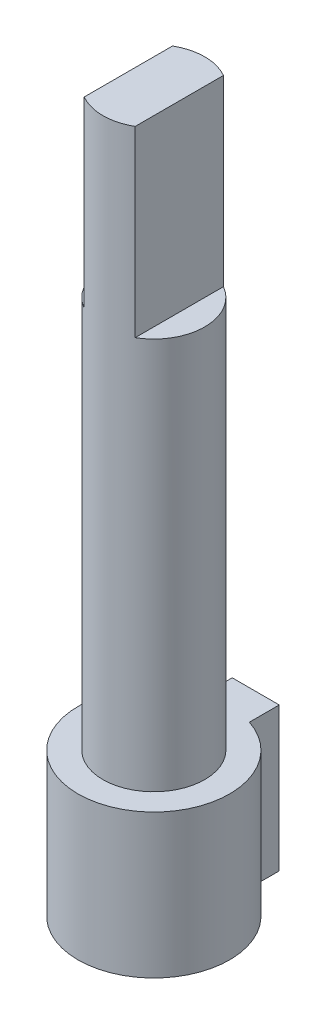
SolidWorks part; units mm, degrees
ref_plane "Front Plane" through (0, 0, 0) normal (0, 0, 1) x (1, 0, 0)
ref_plane "Top Plane" through (0, 0, 0) normal (0, 1, 0) x (1, 0, 0)
ref_plane "Right Plane" through (0, 0, 0) normal (1, 0, 0) x (0, 0, -1)
sketch "Sketch1" plane through (0, 0, 0) normal (0, 1, 0) x (1, 0, 0)
  line L1 (-1, 2.8284) -> (1, 2.8284)
  line L2 (-1, 2.8284) -> (-1, 3.9984)
  line L3 (-1, 3.9984) -> (1, 3.9984)
  line L4 (1, 2.8284) -> (1, 3.9984)
  circle A0 centre (0, 0) radius 3
  point P7 (0, 0)
  point P8 (0, 2.8284)
  dimension "D1" = 6
  dimension "D2" = 1.17
  dimension "D3" = 2
extrude "Boss-Extrude1" add sketch "Sketch1" along normal blind 27.5 contours L1 A0
sketch "Sketch2" plane through (0, 27.5, 0) normal (0, 1, 0) x (1, 0, 0)
  circle A0 centre (0, 0) radius 1.95
  circle A1 centre (0, 0) radius 6.1662
  dimension "D1" = 3.9
extrude "Cut-Extrude1" cut sketch "Sketch2" against normal blind 22
sketch "Sketch3" plane through (0, 27.5, 0) normal (0, 1, 0) x (1, 0, 0)
  line L0 (-0.975, 1.6887) -> (-0.975, -1.6887)
  line L1 (0.975, 1.6887) -> (0.975, -1.6887)
  circle A0 centre (0, 0) radius 1.95 construction
  arc A1 (-0.975, 1.6887) -> (-0.975, -1.6887) centre (0, 0) ccw
  arc A2 (0.975, -1.6887) -> (0.975, 1.6887) centre (0, 0) ccw
  dimension "D1" = 1.95
  dimension "D2" = 0.975
extrude "Cut-Extrude2" cut sketch "Sketch3" against normal blind 7
sketch "Sketch4" plane through (0, 0, 0) normal (0, -1, 0) x (1, 0, 0)
  line L0 (-1, -3.9984) -> (1, -3.9984) construction
  line L1 (1, -2.8284) -> (1, -3.9984) construction
  line L2 (-1, -2.8284) -> (-1, -3.9984) construction
  line L3 (-1, -3.9984) -> (1, -3.9984)
  line L4 (1, -2.8284) -> (1, -3.9984)
  line L5 (-1, -2.8284) -> (-1, -3.9984)
  line L6 (-0.9, -2.7568) -> (-0.9, -3.8984)
  line L7 (-0.9, -3.8984) -> (0.9, -3.8984)
  line L8 (0.9, -2.7568) -> (0.9, -3.8984)
  arc A0 (1, -2.8284) -> (-1, -2.8284) centre (0, 0) ccw construction
  arc A1 (1, -2.8284) -> (-1, -2.8284) centre (0, 0) ccw
  arc A2 (0.9, -2.7568) -> (-0.9, -2.7568) centre (0, 0) ccw
  dimension "D1" = 0.1
extrude "Cut-Extrude3" cut sketch "Sketch4" against normal blind 100
